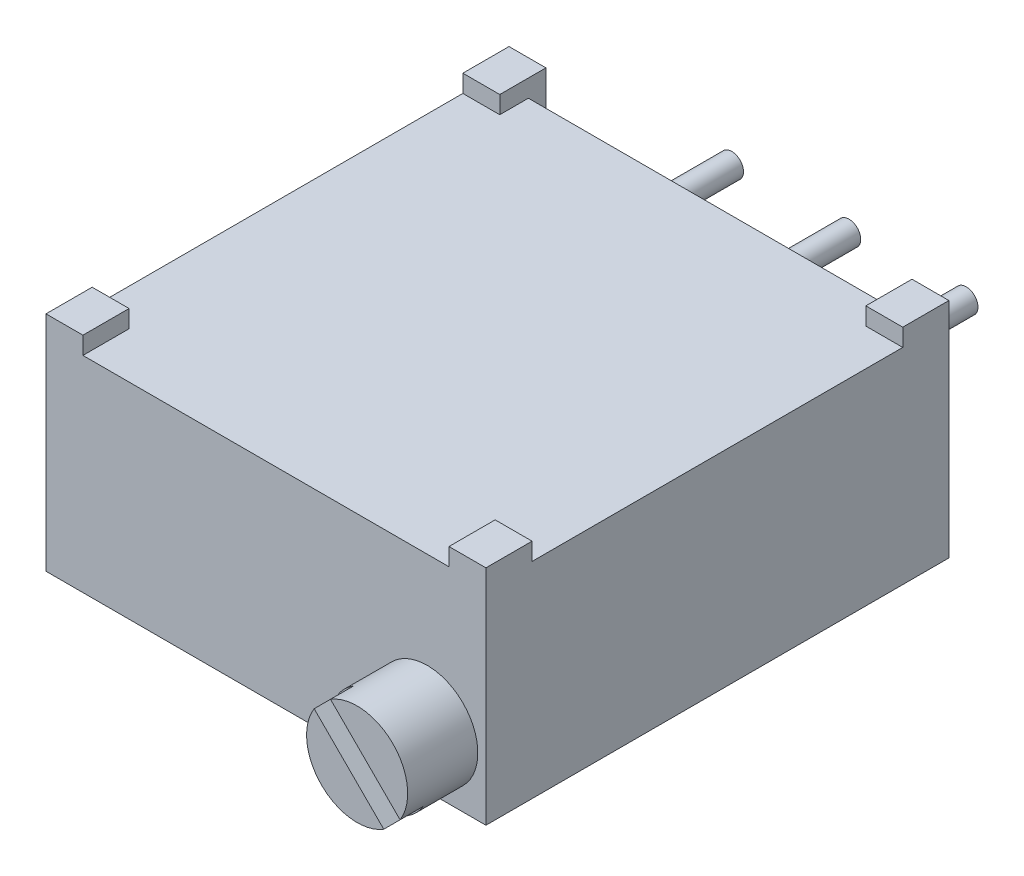
SolidWorks part; units mm, degrees
ref_plane "Plano frontal" through (0, 0, 0) normal (0, 0, 1) x (1, 0, 0)
ref_plane "Plano superior" through (0, 0, 0) normal (0, 1, 0) x (1, 0, 0)
ref_plane "Plano direito" through (0, 0, 0) normal (1, 0, 0) x (0, 0, -1)
sketch "Esboço1" plane through (0, 0, 0) normal (0, 1, 0) x (1, 0, 0)
  line L0 (0, -10.03) -> (0, 0) construction
  line L1 (-4.765, -10.03) -> (4.765, -10.03)
  line L2 (-4.765, -10.03) -> (-4.765, 0)
  line L3 (-4.765, 0) -> (4.765, 0)
  line L4 (4.765, -10.03) -> (4.765, 0)
  dimension "D1" = 9.53
  dimension "D2" = 10.03
extrude "Ressalto-extrusão1" add sketch "Esboço1" along normal mid plane 4.83
sketch "Esboço2" plane through (0, -2.415, 0) normal (0, -1, 0) x (-1, 0, 0)
  line L1 (3.965, 0.62) -> (-3.965, 0.62)
  line L2 (3.965, 0.62) -> (3.965, -0.38)
  line L3 (3.965, -0.38) -> (-3.965, -0.38)
  line L4 (-3.965, 0.62) -> (-3.965, -0.38)
  line L5 (-4.765, 0) -> (4.765, 0) construction
  line L6 (4.765, 0) -> (4.765, -10.03) construction
  line L7 (-4.765, -10.03) -> (-4.765, 0) construction
  dimension "D1" = 0.38
  dimension "D2" = 0.8
  dimension "D3" = 0.8
  dimension "D4" = 1
extrude "Corte-extrusão1" cut sketch "Esboço2" against normal up to next
sketch "Esboço3" plane through (0, 2.415, 0) normal (0, 1, 0) x (1, 0, 0)
  line L0 (3.965, -0.38) -> (-3.965, -0.38)
  line L1 (-3.965, -0.38) -> (-3.965, -1)
  line L3 (-3.965, -1) -> (-4.765, -1)
  line L4 (-4.765, 0) -> (-4.765, -10.03) construction
  line L5 (-4.765, -1) -> (-4.765, -9.03)
  line L7 (-4.765, -9.03) -> (-3.965, -9.03)
  line L8 (-3.965, -9.03) -> (-3.965, -10.03)
  line L9 (-4.765, -10.03) -> (4.765, -10.03) construction
  line L11 (-3.965, -10.03) -> (3.965, -10.03)
  line L12 (3.965, -10.03) -> (3.965, -9.03)
  line L13 (3.965, -9.03) -> (4.765, -9.03)
  line L15 (4.765, -10.03) -> (4.765, 0) construction
  line L16 (4.765, -9.03) -> (4.765, -1)
  line L17 (4.765, -1) -> (3.965, -1)
  line L18 (3.965, -1) -> (3.965, -0.38)
  line L19 (4.765, 0) -> (3.965, 0) construction
  dimension "D1" = 1
  dimension "D2" = 1
extrude "Corte-extrusão2" cut sketch "Esboço3" against normal blind 0.38
sketch "Esboço4" plane through (0, 0, 10.03) normal (0, 0, 1) x (1, 0, 0)
  line L0 (4.765, 2.415) -> (4.765, -2.415) construction
  line L1 (-4.765, -2.415) -> (4.765, -2.415) construction
  circle A0 centre (3.495, -1.145) radius 1.095
  dimension "D3" = 2.19
  dimension "D1" = 1.27
  dimension "D2" = 1.27
extrude "Ressalto-extrusão2" add sketch "Esboço4" along normal blind 1.52
sketch "Esboço5" plane through (0, 0, 11.55) normal (0, 0, 1) x (1, 0, 0)
  line L0 (2.4, -1.145) -> (4.59, -1.145) construction
  line L1 (2.9179, -0.2144) -> (4.4256, -1.7221)
  line L2 (2.5644, -0.5679) -> (4.0721, -2.0756)
  circle A0 centre (3.495, -1.145) radius 1.095 construction
  circle A1 centre (3.495, -1.145) radius 1.095 construction
  arc A2 (4.0721, -2.0756) -> (4.4256, -1.7221) centre (3.495, -1.145) ccw
  arc A3 (2.9179, -0.2144) -> (2.5644, -0.5679) centre (3.495, -1.145) ccw
  dimension "D1" = 0.5
  dimension "D2" = 45
extrude "Corte-extrusão3" cut sketch "Esboço5" against normal blind 0.5
sketch "Esboço6" plane through (0, 0, 0.38) normal (0, 0, -1) x (-1, 0, 0)
  line L0 (-3.965, 2.415) -> (-4.765, 2.415) construction
  line L1 (0, 0.005) -> (0, 0) construction
  line L2 (0, 0.005) -> (-2.54, 0.005) construction
  line L3 (0, 0.005) -> (2.54, 0.005) construction
  circle A0 centre (0, 0.005) radius 0.255
  circle A1 centre (-2.54, 0.005) radius 0.255
  circle A2 centre (2.54, 0.005) radius 0.255
  point P2 (-4.365, 2.415)
  dimension "D2" = 0.51
  dimension "D1" = 2.41
  dimension "D3" = 2.54
  dimension "D4" = 2.54
extrude "Ressalto-extrusão3" add sketch "Esboço6" along normal blind 2.98
